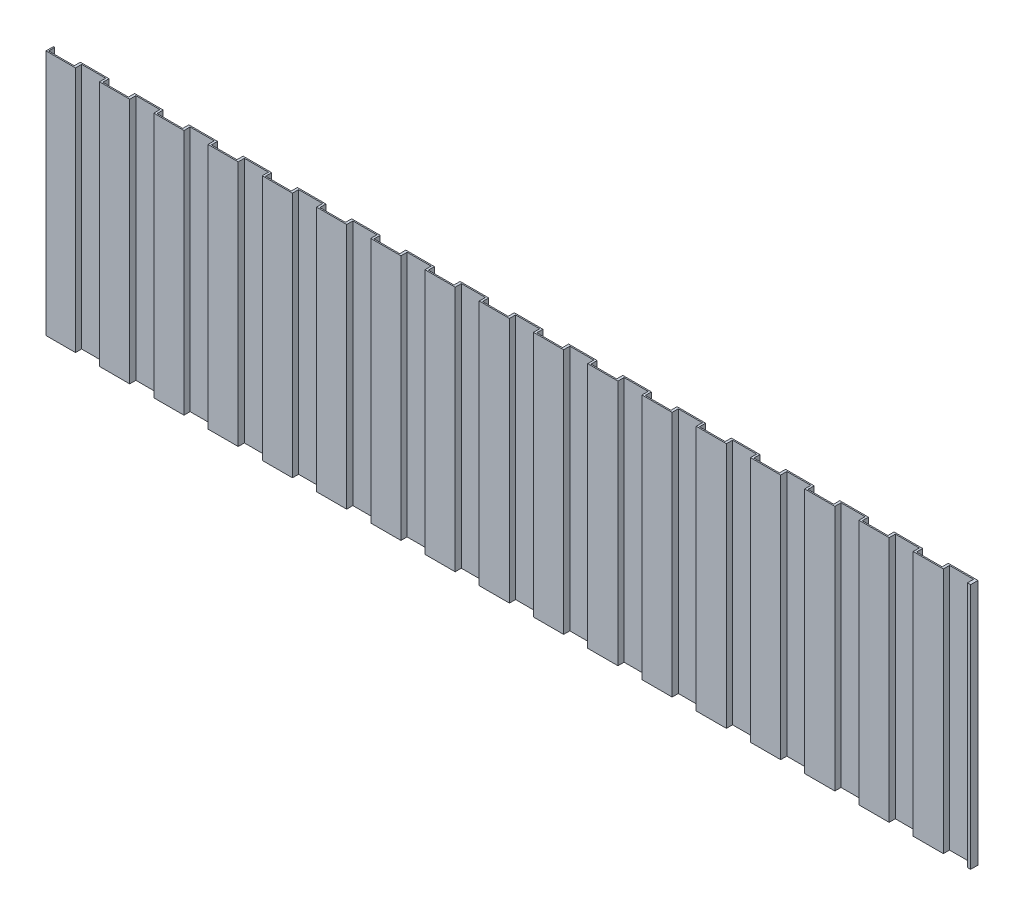
SolidWorks part; units mm, degrees
ref_plane "Front Plane" through (0, 0, 0) normal (0, 0, 1) x (1, 0, 0)
ref_plane "Top Plane" through (0, 0, 0) normal (0, 1, 0) x (1, 0, 0)
ref_plane "Right Plane" through (0, 0, 0) normal (1, 0, 0) x (0, 0, -1)
sketch "Sketch1" plane through (0, 0, 0) normal (0, 0, 1) x (1, 0, 0)
  line L1 (-3750, 2000) -> (3750, 2000)
  line L2 (-3750, 2000) -> (-3750, -2000)
  line L3 (-3750, -2000) -> (3750, -2000)
  line L4 (3750, 2000) -> (3750, -2000)
  line L5 (-3750, 2000) -> (3750, -2000) construction
  line L6 (-3750, -2000) -> (3750, 2000) construction
  point P0 (0, 0)
  dimension "D1" = 7500
  dimension "D2" = 4000
extrude "Boss-Extrude1" add sketch "Sketch1" along normal blind 60
sketch "Sketch2" plane through (0, -2000, 0) normal (0, -1, 0) x (-1, 0, 0)
  line L0 (3750, 0) -> (-3750, 0) construction
  line L1 (3739.0761, 0) -> (3531.0261, 0)
  line L2 (3739.0761, 0) -> (3739.0761, -50)
  line L3 (3739.0761, -50) -> (3531.0261, -50)
  line L4 (3531.0261, 0) -> (3531.0261, -50)
  line L5 (3750, -60) -> (-3750, -60) construction
  line L6 (3510.9951, -60) -> (3315.6922, -60)
  line L7 (3510.9951, -60) -> (3510.9951, -10)
  line L8 (3510.9951, -10) -> (3315.6922, -10)
  line L9 (3315.6922, -60) -> (3315.6922, -10)
  line L10 (3299.0761, -50) -> (3091.0261, -50)
  line L11 (3299.0761, 0) -> (3299.0761, -50)
  line L12 (3299.0761, 0) -> (3091.0261, 0)
  line L13 (3091.0261, 0) -> (3091.0261, -50)
  line L14 (3070.9951, -10) -> (2875.6922, -10)
  line L15 (3070.9951, -60) -> (3070.9951, -10)
  line L16 (3070.9951, -60) -> (2875.6922, -60)
  line L17 (2875.6922, -60) -> (2875.6922, -10)
  line L18 (2859.0761, -50) -> (2651.0261, -50)
  line L19 (2859.0761, 0) -> (2859.0761, -50)
  line L20 (2859.0761, 0) -> (2651.0261, 0)
  line L21 (2651.0261, 0) -> (2651.0261, -50)
  line L22 (2630.9951, -10) -> (2435.6922, -10)
  line L23 (2630.9951, -60) -> (2630.9951, -10)
  line L24 (2630.9951, -60) -> (2435.6922, -60)
  line L25 (2435.6922, -60) -> (2435.6922, -10)
  line L26 (2419.0761, -50) -> (2211.0261, -50)
  line L27 (2419.0761, 0) -> (2419.0761, -50)
  line L28 (2419.0761, 0) -> (2211.0261, 0)
  line L29 (2211.0261, 0) -> (2211.0261, -50)
  line L30 (2190.9951, -10) -> (1995.6922, -10)
  line L31 (2190.9951, -60) -> (2190.9951, -10)
  line L32 (2190.9951, -60) -> (1995.6922, -60)
  line L33 (1995.6922, -60) -> (1995.6922, -10)
  line L34 (1979.0761, -50) -> (1771.0261, -50)
  line L35 (1979.0761, 0) -> (1979.0761, -50)
  line L36 (1979.0761, 0) -> (1771.0261, 0)
  line L37 (1771.0261, 0) -> (1771.0261, -50)
  line L38 (1750.9951, -10) -> (1555.6922, -10)
  line L39 (1750.9951, -60) -> (1750.9951, -10)
  line L40 (1750.9951, -60) -> (1555.6922, -60)
  line L41 (1555.6922, -60) -> (1555.6922, -10)
  line L42 (1539.0761, -50) -> (1331.0261, -50)
  line L43 (1539.0761, 0) -> (1539.0761, -50)
  line L44 (1539.0761, 0) -> (1331.0261, 0)
  line L45 (1331.0261, 0) -> (1331.0261, -50)
  line L46 (1310.9951, -10) -> (1115.6922, -10)
  line L47 (1310.9951, -60) -> (1310.9951, -10)
  line L48 (1310.9951, -60) -> (1115.6922, -60)
  line L49 (1115.6922, -60) -> (1115.6922, -10)
  line L50 (1099.0761, -50) -> (891.0261, -50)
  line L51 (1099.0761, 0) -> (1099.0761, -50)
  line L52 (1099.0761, 0) -> (891.0261, 0)
  line L53 (891.0261, 0) -> (891.0261, -50)
  line L54 (870.9951, -10) -> (675.6922, -10)
  line L55 (870.9951, -60) -> (870.9951, -10)
  line L56 (870.9951, -60) -> (675.6922, -60)
  line L57 (675.6922, -60) -> (675.6922, -10)
  line L58 (659.0761, -50) -> (451.0261, -50)
  line L59 (659.0761, 0) -> (659.0761, -50)
  line L60 (659.0761, 0) -> (451.0261, 0)
  line L61 (451.0261, 0) -> (451.0261, -50)
  line L62 (430.9951, -10) -> (235.6922, -10)
  line L63 (430.9951, -60) -> (430.9951, -10)
  line L64 (430.9951, -60) -> (235.6922, -60)
  line L65 (235.6922, -60) -> (235.6922, -10)
  line L66 (219.0761, -50) -> (11.0261, -50)
  line L67 (219.0761, 0) -> (219.0761, -50)
  line L68 (219.0761, 0) -> (11.0261, 0)
  line L69 (11.0261, 0) -> (11.0261, -50)
  line L70 (-9.0049, -10) -> (-204.3078, -10)
  line L71 (-9.0049, -60) -> (-9.0049, -10)
  line L72 (-9.0049, -60) -> (-204.3078, -60)
  line L73 (-204.3078, -60) -> (-204.3078, -10)
  line L74 (-220.9239, -50) -> (-428.9739, -50)
  line L75 (-220.9239, 0) -> (-220.9239, -50)
  line L76 (-220.9239, 0) -> (-428.9739, 0)
  line L77 (-428.9739, 0) -> (-428.9739, -50)
  line L78 (-449.0049, -10) -> (-644.3078, -10)
  line L79 (-449.0049, -60) -> (-449.0049, -10)
  line L80 (-449.0049, -60) -> (-644.3078, -60)
  line L81 (-644.3078, -60) -> (-644.3078, -10)
  line L82 (-660.9239, -50) -> (-868.9739, -50)
  line L83 (-660.9239, 0) -> (-660.9239, -50)
  line L84 (-660.9239, 0) -> (-868.9739, 0)
  line L85 (-868.9739, 0) -> (-868.9739, -50)
  line L86 (-889.0049, -10) -> (-1084.3078, -10)
  line L87 (-889.0049, -60) -> (-889.0049, -10)
  line L88 (-889.0049, -60) -> (-1084.3078, -60)
  line L89 (-1084.3078, -60) -> (-1084.3078, -10)
  line L90 (-1100.9239, -50) -> (-1308.9739, -50)
  line L91 (-1100.9239, 0) -> (-1100.9239, -50)
  line L92 (-1100.9239, 0) -> (-1308.9739, 0)
  line L93 (-1308.9739, 0) -> (-1308.9739, -50)
  line L94 (-1329.0049, -10) -> (-1524.3078, -10)
  line L95 (-1329.0049, -60) -> (-1329.0049, -10)
  line L96 (-1329.0049, -60) -> (-1524.3078, -60)
  line L97 (-1524.3078, -60) -> (-1524.3078, -10)
  line L98 (-1540.9239, -50) -> (-1748.9739, -50)
  line L99 (-1540.9239, 0) -> (-1540.9239, -50)
  line L100 (-1540.9239, 0) -> (-1748.9739, 0)
  line L101 (-1748.9739, 0) -> (-1748.9739, -50)
  line L102 (-1769.0049, -10) -> (-1964.3078, -10)
  line L103 (-1769.0049, -60) -> (-1769.0049, -10)
  line L104 (-1769.0049, -60) -> (-1964.3078, -60)
  line L105 (-1964.3078, -60) -> (-1964.3078, -10)
  line L106 (-1980.9239, -50) -> (-2188.9739, -50)
  line L107 (-1980.9239, 0) -> (-1980.9239, -50)
  line L108 (-1980.9239, 0) -> (-2188.9739, 0)
  line L109 (-2188.9739, 0) -> (-2188.9739, -50)
  line L110 (-2209.0049, -10) -> (-2404.3078, -10)
  line L111 (-2209.0049, -60) -> (-2209.0049, -10)
  line L112 (-2209.0049, -60) -> (-2404.3078, -60)
  line L113 (-2404.3078, -60) -> (-2404.3078, -10)
  line L114 (-2420.9239, -50) -> (-2628.9739, -50)
  line L115 (-2420.9239, 0) -> (-2420.9239, -50)
  line L116 (-2420.9239, 0) -> (-2628.9739, 0)
  line L117 (-2628.9739, 0) -> (-2628.9739, -50)
  line L118 (-2649.0049, -10) -> (-2844.3078, -10)
  line L119 (-2649.0049, -60) -> (-2649.0049, -10)
  line L120 (-2649.0049, -60) -> (-2844.3078, -60)
  line L121 (-2844.3078, -60) -> (-2844.3078, -10)
  line L122 (-2860.9239, -50) -> (-3068.9739, -50)
  line L123 (-2860.9239, 0) -> (-2860.9239, -50)
  line L124 (-2860.9239, 0) -> (-3068.9739, 0)
  line L125 (-3068.9739, 0) -> (-3068.9739, -50)
  line L126 (-3089.0049, -10) -> (-3284.3078, -10)
  line L127 (-3089.0049, -60) -> (-3089.0049, -10)
  line L128 (-3089.0049, -60) -> (-3284.3078, -60)
  line L129 (-3284.3078, -60) -> (-3284.3078, -10)
  line L130 (-3300.9239, -50) -> (-3508.9739, -50)
  line L131 (-3300.9239, 0) -> (-3300.9239, -50)
  line L132 (-3300.9239, 0) -> (-3508.9739, 0)
  line L133 (-3508.9739, 0) -> (-3508.9739, -50)
  line L134 (-3529.0049, -10) -> (-3724.3078, -10)
  line L135 (-3529.0049, -60) -> (-3529.0049, -10)
  line L136 (-3529.0049, -60) -> (-3724.3078, -60)
  line L137 (-3724.3078, -60) -> (-3724.3078, -10)
  dimension "D1" = 10
  dimension "D2" = 10
  dimension "D3" = 17
extrude "Cut-Extrude1" cut sketch "Sketch2" against normal blind 5107
sketch "Sketch3" plane through (0, 0, 60) normal (0, 0, 1) x (1, 0, 0)
  line L1 (-3947.8066, 0) -> (4908.6878, 0)
  line L2 (-3947.8066, 0) -> (-3947.8066, -2648.0099)
  line L3 (-3947.8066, -2648.0099) -> (4908.6878, -2648.0099)
  line L4 (4908.6878, 0) -> (4908.6878, -2648.0099)
extrude "Cut-Extrude2" cut sketch "Sketch3" against normal blind 887
